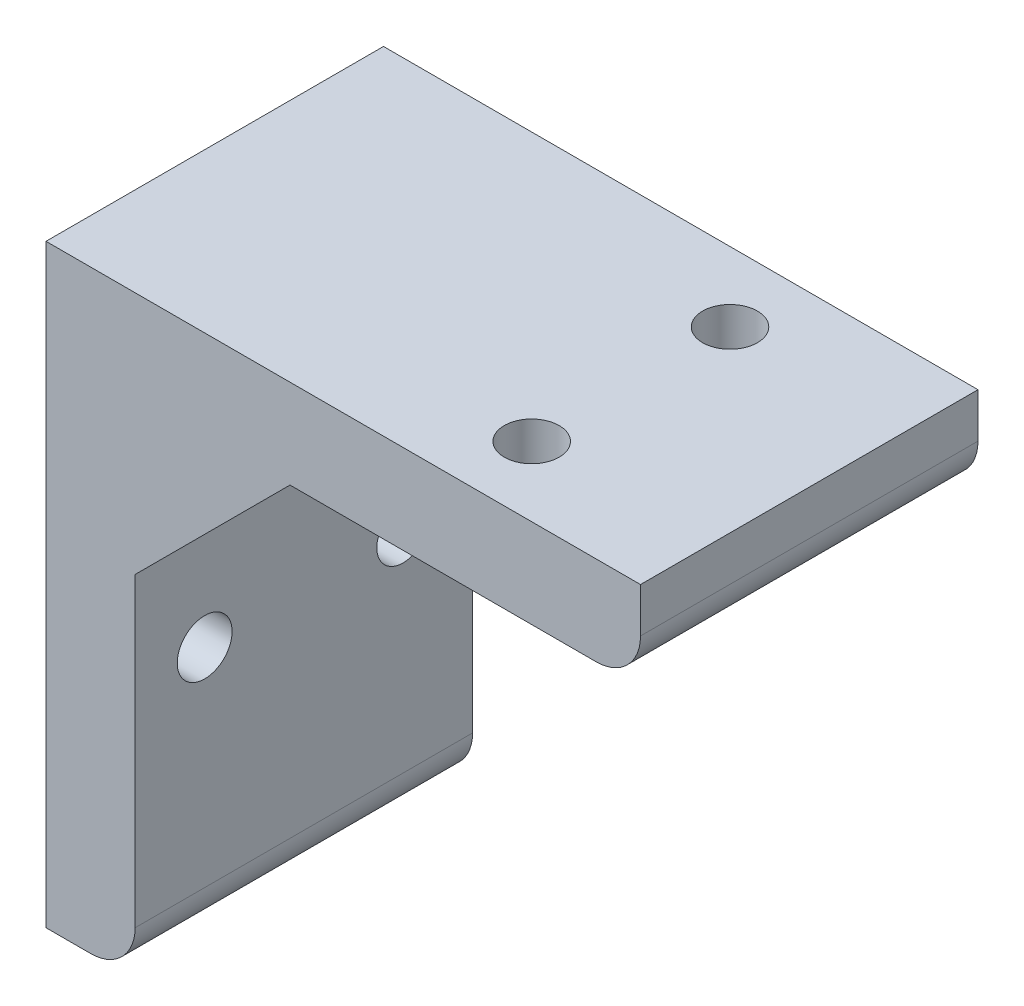
SolidWorks part; units mm, degrees
ref_plane "Front Plane" through (0, 0, 0) normal (0, 0, 1) x (1, 0, 0)
ref_plane "Top Plane" through (0, 0, 0) normal (0, 1, 0) x (1, 0, 0)
ref_plane "Right Plane" through (0, 0, 0) normal (1, 0, 0) x (0, 0, -1)
sketch "Sketch1" plane through (0, 0, 0) normal (1, 0, 0) x (0, 0, -1)
  line L1 (-17.0307, -30) -> (17.0307, -30)
  line L2 (-17.0307, -30) -> (-17.0307, 30)
  line L3 (-17.0307, 30) -> (17.0307, 30)
  line L4 (17.0307, -30) -> (17.0307, 30)
  line L5 (-17.0307, -30) -> (17.0307, 30) construction
  line L6 (-17.0307, 30) -> (17.0307, -30) construction
  point P0 (0, 0)
  dimension "D1" = 34.0614
  dimension "D2" = 60
extrude "Boss-Extrude1" add sketch "Sketch1" along normal blind 8.9916
sketch "Sketch2" plane through (8.9916, 0, 0) normal (1, 0, 0) x (0, 0, -1)
  line L0 (17.0307, -30) -> (17.0307, 30) construction
  line L1 (-17.0307, 30) -> (17.0307, 30)
  line L2 (-17.0307, 30) -> (-17.0307, 21.0084)
  line L3 (-17.0307, 21.0084) -> (17.0307, 21.0084)
  line L4 (17.0307, 30) -> (17.0307, 21.0084)
  dimension "D1" = 8.9916
extrude "Boss-Extrude2" add sketch "Sketch2" along normal blind 51.0084
sketch "Sketch3" plane through (60, 0, 0) normal (1, 0, 0) x (0, 0, -1)
  line L0 (0, 30) -> (0, 21.0084) construction
  line L1 (17.0307, 30) -> (-17.0307, 30) construction
  line L2 (-17.0307, 21.0084) -> (17.0307, 21.0084) construction
  line L4 (0, 30) -> (17.0307, 30)
  line L5 (0, 30) -> (0, 21.0084)
  line L6 (0, 21.0084) -> (17.0307, 21.0084)
  line L7 (17.0307, 30) -> (17.0307, 21.0084)
sketch "Sketch5" plane through (8.9916, 0, 0) normal (1, 0, 0) x (0, 0, -1)
  line L0 (-10.0076, -30) -> (-10.0076, 21.0084) construction
  line L3 (-17.0307, -4.4958) -> (17.0307, -4.4958) construction
  line L4 (-17.0307, 21.0084) -> (-17.0307, -30) construction
  line L5 (17.0307, -30) -> (17.0307, 21.0084) construction
  line L6 (-17.0307, -30) -> (17.0307, -30) construction
  line L7 (-17.0307, 21.0084) -> (17.0307, 21.0084) construction
  line L8 (10.0076, -30) -> (10.0076, 21.0084) construction
  circle A0 centre (-10.0076, -4.4958) radius 2.7686
  circle A1 centre (10.0076, -4.4958) radius 2.6416
  dimension "D3" = 5.5372
  dimension "D4" = 5.2832
  dimension "D1" = 7.0231
  dimension "D2" = 7.0231
extrude "Cut-Extrude2" cut sketch "Sketch5" against normal up to next
sketch "Sketch6" plane through (0, 30, 0) normal (0, 1, 0) x (1, 0, 0)
  line L0 (41.9957, 17.0307) -> (41.9957, -17.0307) construction
  line L1 (60, 17.0307) -> (0, 17.0307) construction
  line L2 (60, -17.0307) -> (0, -17.0307) construction
  line L3 (60, 0) -> (60, 17.0307) construction
  line L4 (0, 10.0076) -> (60, 10.0076) construction
  line L5 (0, 17.0307) -> (0, -17.0307) construction
  line L6 (0, -10.0076) -> (60, -10.0076) construction
  line L7 (60, 17.0307) -> (60, -17.0307) construction
  circle A0 centre (41.9957, 10.0076) radius 2.7686
  circle A1 centre (41.9957, -10.0076) radius 2.7686
  point P16 (41.9957, 10.0076)
  point P17 (41.9957, -10.0076)
  dimension "D4" = 5.5372
  dimension "D5" = 5.5372
  dimension "D1" = 18.0043
  dimension "D2" = 7.0231
  dimension "D3" = 7.0231
extrude "Cut-Extrude3" cut sketch "Sketch6" against normal up to next
sketch "Sketch7" plane through (0, 0, 17.0307) normal (0, 0, 1) x (1, 0, 0)
  line L0 (8.9916, 21.0084) -> (8.9916, 5.3745)
  line L1 (8.9916, 21.0084) -> (8.9916, -30) construction
  line L2 (8.9916, 5.3745) -> (24.6255, 21.0084)
  line L3 (60, 21.0084) -> (8.9916, 21.0084) construction
  line L4 (24.6255, 21.0084) -> (8.9916, 21.0084)
extrude "Boss-Extrude3" add sketch "Sketch7" against normal up to surface (34.0614 mm away) up to face at (27.2479, 2.7521, -17.0307)
fillet "Fillet1" radius 4.4958 2 edges at (8.9916, -30, 0) (60, 21.0084, 0)
